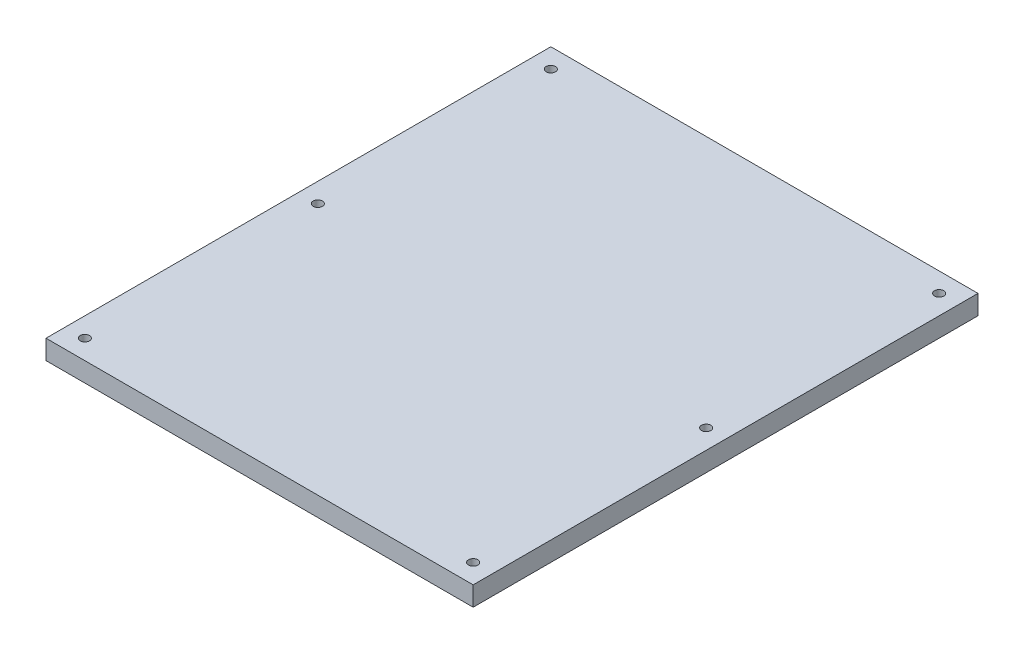
SolidWorks part; units mm, degrees
ref_plane "Front Plane" through (0, 0, 0) normal (0, 0, 1) x (1, 0, 0)
ref_plane "Top Plane" through (0, 0, 0) normal (0, 1, 0) x (1, 0, 0)
ref_plane "Right Plane" through (0, 0, 0) normal (1, 0, 0) x (0, 0, -1)
sketch "Sketch1" plane through (0, 0, 0) normal (0, 1, 0) x (1, 0, 0)
  line L1 (-43.4986, 24.7295) -> (96.2014, 24.7295)
  line L2 (-43.4986, 24.7295) -> (-43.4986, -140.3705)
  line L3 (-43.4986, -140.3705) -> (96.2014, -140.3705)
  line L4 (96.2014, 24.7295) -> (96.2014, -140.3705)
  dimension "D1" = 139.7
  dimension "D2" = 165.1
extrude "Extrude1" add sketch "Sketch1" along normal blind 6.35
sketch "Sketch2" plane through (0, 6.35, 0) normal (0, 1, 0) x (1, 0, 0)
  line L0 (-43.4986, 24.7295) -> (-43.4986, -140.3705) construction
  line L1 (96.2014, 24.7295) -> (-43.4986, 24.7295) construction
  line L2 (96.2014, -140.3705) -> (96.2014, 24.7295) construction
  line L3 (-43.4986, -140.3705) -> (96.2014, -140.3705) construction
  circle A0 centre (-37.1486, 18.3795) radius 1.524
  circle A1 centre (-37.1486, -57.8205) radius 1.524
  circle A2 centre (89.8514, 18.3795) radius 1.524
  circle A3 centre (89.8514, -134.0205) radius 1.524
  circle A4 centre (89.8514, -57.8205) radius 1.524
  circle A5 centre (-37.1486, -134.0205) radius 1.524
  point P20 (-43.4986, -57.8205)
  dimension "D5" = 3.048
  dimension "D1" = 6.35
  dimension "D2" = 6.35
  dimension "D3" = 6.35
  dimension "D4" = 6.35
extrude "Cut-Extrude1" cut sketch "Sketch2" against normal through all
